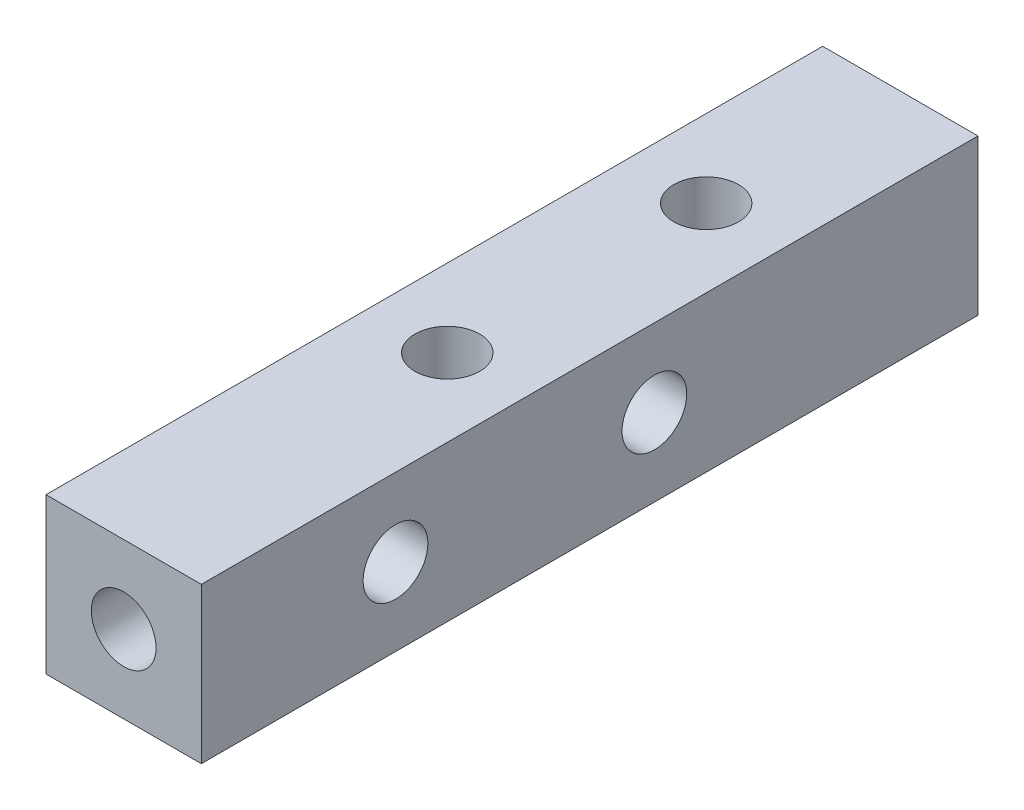
SolidWorks part; units mm, degrees
ref_plane "前视基准面" through (0, 0, 0) normal (0, 0, 1) x (1, 0, 0)
ref_plane "上视基准面" through (0, 0, 0) normal (0, 1, 0) x (1, 0, 0)
ref_plane "右视基准面" through (0, 0, 0) normal (1, 0, 0) x (0, 0, -1)
other "Configuration Table"
sketch "草图1" plane through (0, 0, 0) normal (1, 0, 0) x (0, 0, -1)
  line L1 (0, 0) -> (30, 0)
  line L2 (0, 0) -> (0, 6)
  line L3 (0, 6) -> (30, 6)
  line L4 (30, 0) -> (30, 6)
  dimension "D1" = 30
  dimension "D2" = 6
extrude "凸台-拉伸1" add sketch "草图1" along normal blind 6
hole_wizard "M3 螺纹孔1" positions "草图3" profile "草图4" tap size "M3" standard "GB" end condition through all
sketch "草图3" plane through (0, 0, 0) normal (0, 0, 1) x (1, 0, 0)
  line L0 (6, 6) -> (6, 0) construction
  line L1 (6, 0) -> (0, 0) construction
  point P0 (3, 3)
  dimension "D1" = 3
  dimension "D2" = 3
sketch "草图4" plane through (3, 3, 0) normal (1, 0, 0) x (0, -1, 0)
  line L0 (0, 0) -> (0, 30)
  line L1 (0, 30) -> (1.25, 30)
  line L2 (1.25, 30) -> (1.25, 0)
  line L5 (1.25, 0) -> (0, 0)
  line L11 (0, -6.35) -> (0, 107.95) construction
  dimension "通孔螺纹孔钻头直径" = 2.5
  dimension "通孔螺纹孔钻头深度" = 30
cosmetic thread "孔螺蚊线1"
hole_wizard "M3 螺纹孔2" positions "草图5" profile "草图6" tap size "M3" standard "GB" end condition through all
sketch "草图5" plane through (0, 6, 0) normal (0, 1, 0) x (1, 0, 0)
  line L0 (6, 0) -> (0, 0) construction
  line L1 (6, 30) -> (0, 30) construction
  line L2 (3, 30) -> (3, 0) construction
  point P0 (3, 12.5)
  point P2 (3, 22.5)
  dimension "D1" = 12.5
  dimension "D2" = 7.5
sketch "草图6" plane through (3, 6, -12.5) normal (1, 0, 0) x (0, 0, 1)
  line L0 (0, 0) -> (0, 6)
  line L1 (0, 6) -> (1.25, 6)
  line L2 (1.25, 6) -> (1.25, 0)
  line L5 (1.25, 0) -> (0, 0)
  line L11 (0, -6.35) -> (0, 107.95) construction
  dimension "通孔螺纹孔钻头直径" = 2.5
  dimension "通孔螺纹孔钻头深度" = 6
cosmetic thread "孔螺蚊线2"
cosmetic thread "孔螺蚊线3"
hole_wizard "M3 螺纹孔3" positions "草图7" profile "草图8" tap size "M3" standard "GB" end condition through all
sketch "草图7" plane through (6, 0, 0) normal (1, 0, 0) x (0, 0, -1)
  line L0 (0, 3) -> (30, 3) construction
  line L1 (0, 6) -> (0, 0) construction
  line L2 (30, 0) -> (30, 6) construction
  point P9 (7.5, 3)
  point P11 (17.5, 3)
  dimension "D1" = 7.5
  dimension "D2" = 12.5
sketch "草图8" plane through (6, 3, -17.5) normal (0, 1, 0) x (0, 0, -1)
  line L0 (0, 0) -> (0, 6)
  line L1 (0, 6) -> (1.25, 6)
  line L2 (1.25, 6) -> (1.25, 0)
  line L5 (1.25, 0) -> (0, 0)
  line L11 (0, -6.35) -> (0, 107.95) construction
  dimension "通孔螺纹孔钻头直径" = 2.5
  dimension "通孔螺纹孔钻头深度" = 6
cosmetic thread "孔螺蚊线4"
cosmetic thread "孔螺蚊线5"
